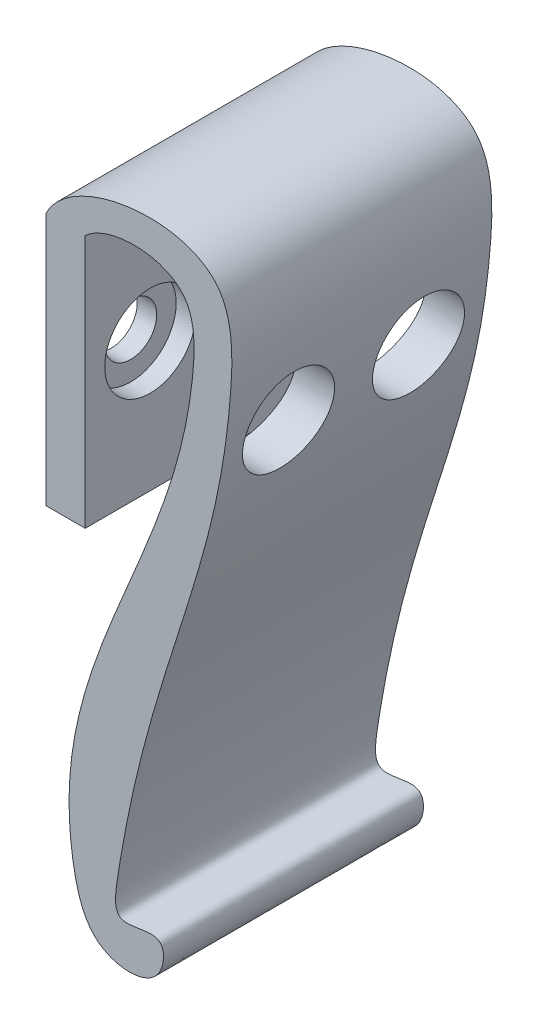
SolidWorks part; units mm, degrees
ref_plane "Front Plane" through (0, 0, 0) normal (0, 0, 1) x (1, 0, 0)
ref_plane "Top Plane" through (0, 0, 0) normal (0, 1, 0) x (1, 0, 0)
ref_plane "Right Plane" through (0, 0, 0) normal (1, 0, 0) x (0, 0, -1)
sketch "Sketch1" plane through (0, 0, 0) normal (0, 0, 1) x (1, 0, 0)
  line L0 (0, 0) -> (0, -50) construction
  line L3 (0, 0) -> (-3, 0)
  line L4 (0, 0) -> (0, -19.4996)
  line L5 (0, -19.4996) -> (-3, -19.4996)
  line L6 (-3, 0) -> (-3, -19.4996)
  line L7 (0, 0) -> (-3, -19.4996) construction
  line L8 (0, -19.4996) -> (-3, 0) construction
  spline S0 degree 3 poles (0, 0) (1.756, 1.6727) (8.497, 1.7538) (8.316, -17.9264) (-4.6398, -30.1594) (0.4178, -47.6626) (5.9613, -47.5436) (6.2355, -43.1138) (1.9794, -45.1415) (4.6165, -25.8165) (11.0632, -17.2126) (11.5373, 5.7282) (-1.1609, 3.8237) (-3, 0) knots 0 0 0 0 0.062552 0.10042 0.404902 0.445151 0.478424 0.493844 0.517517 0.537515 0.83456 0.886834 1 1 1 1
  point P19 (-1.5, -9.7498)
  dimension "D1" = 50
  dimension "D2" = 3
extrude "Boss-Extrude1" add sketch "Sketch1" along normal blind 20 contours L3 S0 | L3 L6 L5 L4
sketch "Sketch2" plane through (-3, 0, 0) normal (-1, 0, 0) x (0, 0, 1)
  line L0 (0, 0) -> (0, -19.4996) construction
  line L2 (20, -19.4996) -> (0, -19.4996) construction
  circle A0 centre (5, -9.4996) radius 2
  circle A1 centre (15, -9.4996) radius 2
  dimension "D1" = 4
  dimension "D2" = 4
  dimension "D3" = 5
  dimension "D4" = 10
  dimension "D5" = 10
  dimension "D6" = 10
extrude "Cut-Extrude1" cut sketch "Sketch2" against normal blind 20
sketch "Sketch3" plane through (0, 0, 0) normal (1, 0, 0) x (0, 0, -1)
  circle A0 centre (-15, -9.4996) radius 3.5
  circle A1 centre (-5, -9.4996) radius 3.5
  circle M1 centre (-5, -9.4996) radius 2
  dimension "D1" = 7
  dimension "D2" = 7
extrude "Cut-Extrude2" cut sketch "Sketch3" along normal blind 20 and the other way blind 1.5 contours A1 M1 | A0
